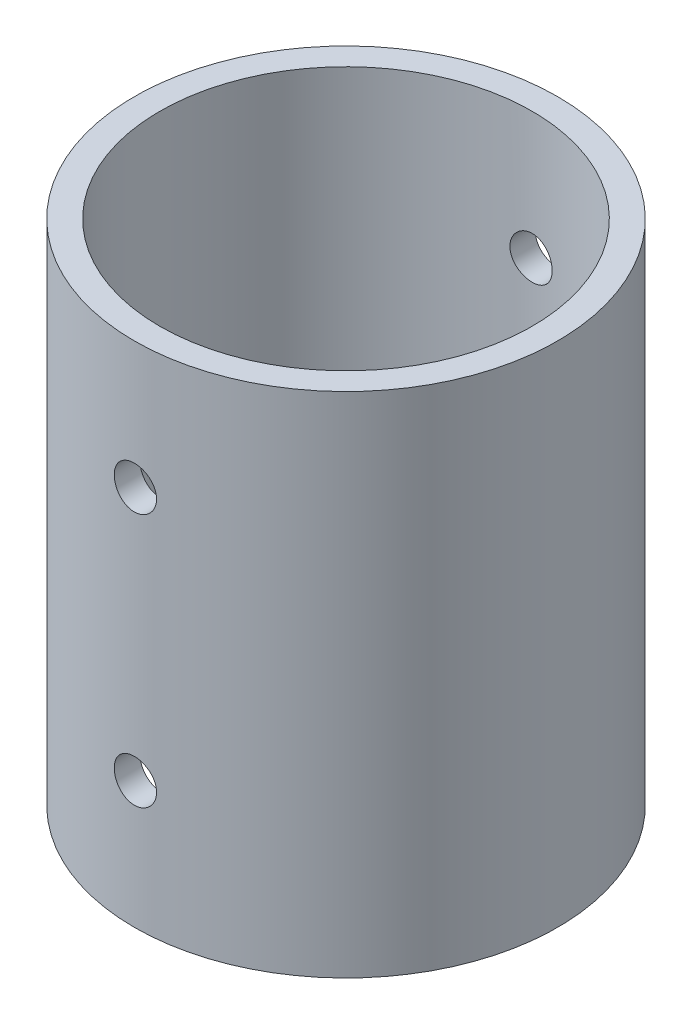
SolidWorks part; units mm, degrees
material "PVC Rígido"
ref_plane "Plano frontal" through (0, 0, 0) normal (0, 0, 1) x (1, 0, 0)
ref_plane "Plano superior" through (0, 0, 0) normal (0, 1, 0) x (1, 0, 0)
ref_plane "Plano direito" through (0, 0, 0) normal (1, 0, 0) x (0, 0, -1)
sketch "Esboço1" plane through (0, 0, 0) normal (0, 1, 0) x (1, 0, 0)
  circle A0 centre (0, 0) radius 22
  circle A1 centre (0, 0) radius 25
  dimension "D1" = 44
  dimension "D2" = 50
extrude "Ressalto-extrusão1" add sketch "Esboço1" along normal blind 60
sketch "Esboço2" plane through (0, 0, 0) normal (0, 0, 1) x (1, 0, 0)
  circle A0 centre (0, 15) radius 2.5
  dimension "D1" = 5
  dimension "D2" = 15
extrude "Corte-extrusão1" cut sketch "Esboço2" against normal through all both and the other way through all
sketch "Esboço3" plane through (0, 0, 0) normal (1, 0, 0) x (0, 0, -1)
  circle A0 centre (0, 15) radius 2.5
  dimension "D2" = 5
  dimension "D1" = 15
extrude "Corte-extrusão2" [suppressed] cut sketch "Esboço3" against normal through all both and the other way through all
ref_plane "Plano1" through (0, 30, 0) normal (0, -1, 0) x (-1, 0, 0)
mirror "Espelhar1" about plane through (0, 30, 0) normal (0, -1, 0) of "Corte-extrusão1", "Corte-extrusão2"
